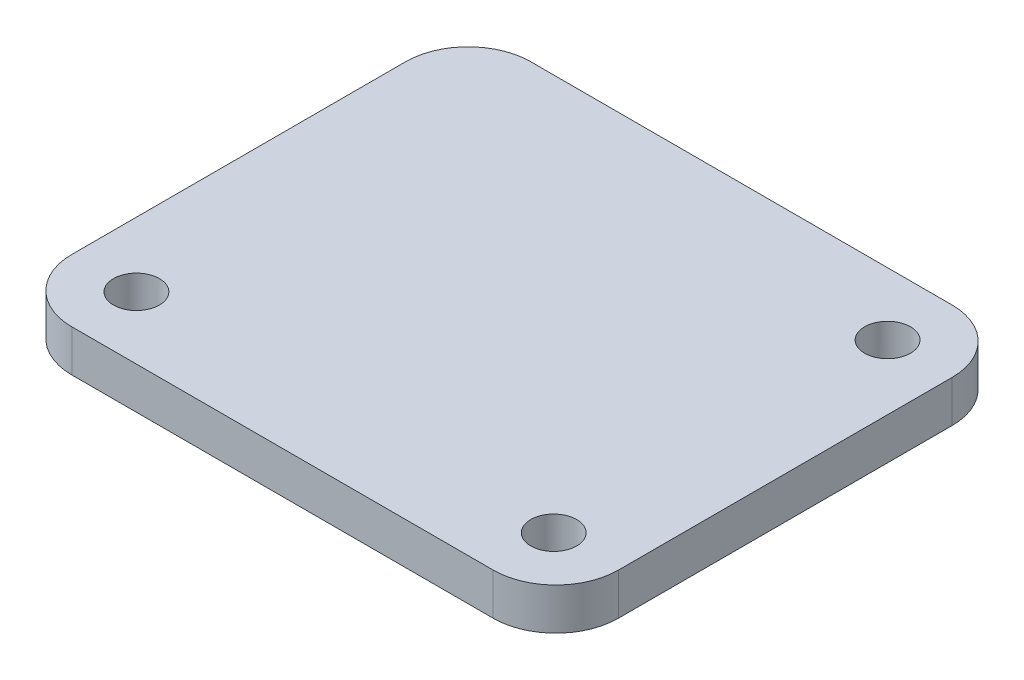
SolidWorks part; units mm, degrees
ref_plane "Front Plane" through (0, 0, 0) normal (0, 0, 1) x (1, 0, 0)
ref_plane "Top Plane" through (0, 0, 0) normal (0, 1, 0) x (1, 0, 0)
ref_plane "Right Plane" through (0, 0, 0) normal (1, 0, 0) x (0, 0, -1)
sketch "Sketch1" plane through (0, 0, 0) normal (0, 1, 0) x (1, 0, 0)
  line L1 (-16.637, -13.97) -> (16.637, -13.97)
  line L2 (-16.637, -13.97) -> (-16.637, 13.97)
  line L3 (-16.637, 13.97) -> (16.637, 13.97)
  line L4 (16.637, -13.97) -> (16.637, 13.97)
  line L5 (-16.637, -13.97) -> (16.637, 13.97) construction
  line L6 (-16.637, 13.97) -> (16.637, -13.97) construction
  point P0 (0, 0)
  dimension "D1" = 33.274
  dimension "D2" = 27.94
extrude "Boss-Extrude1" add sketch "Sketch1" along normal blind 2.54
sketch "Sketch2" plane through (0, 2.54, 0) normal (0, 1, 0) x (1, 0, 0)
  circle A4 centre (12.7, -10.16) radius 1.397
  circle A5 centre (-12.7, -10.16) radius 1.397
  circle A7 centre (12.7, 10.16) radius 1.397
  circle A8 centre (-12.7, 10.16) radius 1.397
  dimension "D1" = 2
  dimension "D2" = 2
extrude "Cut-Extrude1" cut sketch "Sketch2" against normal up to surface (2.54 mm away) up to face at (0, 0, 0)
fillet "Fillet1" radius 3.81 4 edges at (-16.637, 1.27, 13.97) (16.637, 1.27, 13.97) (16.637, 1.27, -13.97) (-16.637, 1.27, -13.97)
